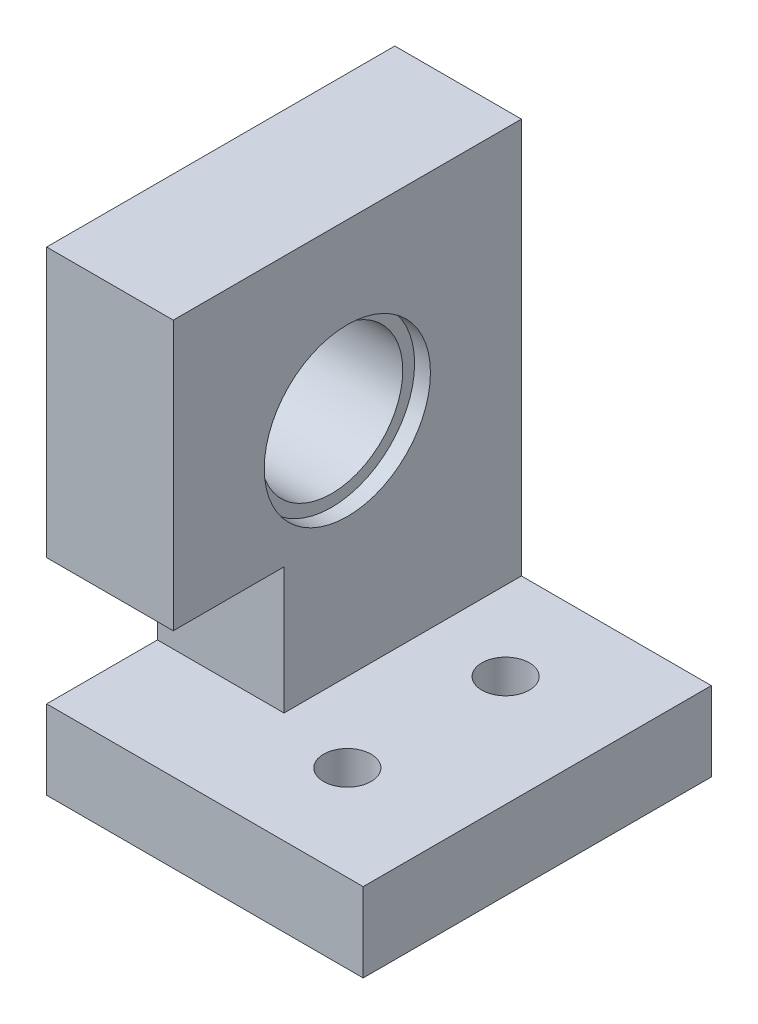
SolidWorks part; units mm, degrees
material "1060 合金"
ref_plane "前视基准面" through (0, 0, 0) normal (0, 0, 1) x (1, 0, 0)
ref_plane "上视基准面" through (0, 0, 0) normal (0, 1, 0) x (1, 0, 0)
ref_plane "右视基准面" through (0, 0, 0) normal (1, 0, 0) x (0, 0, -1)
sketch "草图1" plane through (0, 0, 0) normal (1, 0, 0) x (0, 0, -1)
  line L0 (0, 15) -> (0, 4) construction
  line L1 (-11, 15) -> (11, 15)
  line L2 (-11, 15) -> (-11, -15)
  line L3 (-11, -15) -> (11, -15)
  line L4 (11, 15) -> (11, -15)
  line L5 (-11, 15) -> (11, -15) construction
  line L6 (-11, -15) -> (11, 15) construction
  circle A0 centre (0, 4) radius 4.5
  circle A1 centre (0, 4) radius 5.25
  point P0 (0, 0)
  dimension "D4" = 9
  dimension "D5" = 10.5
  dimension "D1" = 30
  dimension "D2" = 22
  dimension "D3" = 11
extrude "凸台-拉伸1" add sketch "草图1" along normal blind 8 contours L2 L1 L4 L3
sketch "草图2" plane through (0, 0, 0) normal (-1, 0, 0) x (0, 0, 1)
  line L0 (0, 15) -> (0, 4) construction
  line L1 (11, 15) -> (-11, 15) construction
  circle A0 centre (0, 4) radius 4.5
  dimension "D2" = 9
  dimension "D1" = 11
extrude "切除-拉伸1" cut sketch "草图2" against normal through all
sketch "草图3" plane through (0, 0, 0) normal (-1, 0, 0) x (0, 0, 1)
  line L0 (11, -15) -> (11, -10) construction
  line L1 (11, 15) -> (11, -15) construction
  line L3 (11, -10) -> (4, -10)
  line L4 (11, -10) -> (11, -2)
  line L5 (11, -2) -> (4, -2)
  line L6 (4, -10) -> (4, -2)
  dimension "D1" = 5
  dimension "D2" = 7
  dimension "D3" = 8
extrude "切除-拉伸2" cut sketch "草图3" against normal through all
sketch "草图4" plane through (0, 0, 0) normal (-1, 0, 0) x (0, 0, 1)
  circle A0 centre (0, 4) radius 5.25
  dimension "D1" = 10.5
extrude "切除-拉伸3" cut sketch "草图4" against normal blind 1
sketch "草图5" plane through (8, 0, 0) normal (1, 0, 0) x (0, 0, -1)
  circle A0 centre (0, 4) radius 5.25
  dimension "D1" = 10.5
extrude "切除-拉伸4" cut sketch "草图5" against normal blind 1
sketch "草图6" plane through (8, 0, 0) normal (1, 0, 0) x (0, 0, -1)
  line L1 (-11, -10) -> (11, -10)
  line L2 (-11, -10) -> (-11, -15)
  line L3 (-11, -15) -> (11, -15)
  line L4 (11, -10) -> (11, -15)
extrude "凸台-拉伸2" add sketch "草图6" along normal blind 12
sketch "草图7" plane through (0, -15, 0) normal (0, -1, 0) x (1, 0, 0)
  line L0 (20, -11) -> (20, -5) construction
  line L1 (20, 11) -> (20, -11) construction
  line L2 (20, -5) -> (13, -5) construction
  line L10 (9.8, -5) -> (11.4, -7.7713)
  line L11 (11.4, -7.7713) -> (14.6, -7.7713)
  line L12 (14.6, -7.7713) -> (16.2, -5)
  line L13 (16.2, -5) -> (14.6, -2.2287)
  line L14 (14.6, -2.2287) -> (11.4, -2.2287)
  line L15 (11.4, -2.2287) -> (9.8, -5)
  circle A0 centre (13, -5) radius 2.7713 construction
  point P5 (0, 0)
  point P14 (0, 0)
  dimension "D1" = 6
  dimension "D2" = 7
  dimension "D3" = 3.2
  dimension "D4" = 3.8
extrude "切除-拉伸5" cut sketch "草图7" against normal blind 2.5
pattern_linear "阵列(线性)1" count 2 spacing 10 along (0, 0, 1) of "切除-拉伸5"
sketch "草图8" plane through (0, -12.5, 0) normal (0, -1, 0) x (1, 0, 0)
  line L0 (20, 11) -> (20, -11) construction
  line L1 (20, 11) -> (0, 11) construction
  circle A0 centre (13, 5) radius 1.5
  dimension "D1" = 7
  dimension "D2" = 3
  dimension "D3" = 6
extrude "切除-拉伸6" cut sketch "草图8" against normal through all
pattern_linear "阵列(线性)2" count 2 spacing 10 along (0, 0, -1) of "切除-拉伸6"
